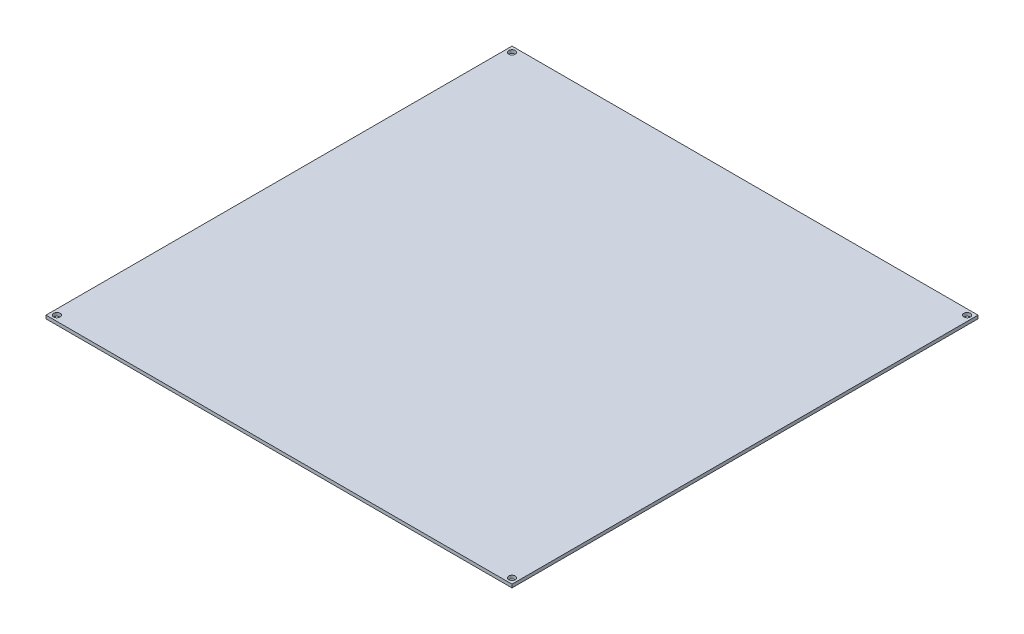
SolidWorks part; units mm, degrees
ref_plane "Plan de face" through (0, 0, 0) normal (0, 0, 1) x (1, 0, 0)
ref_plane "Plan de dessus" through (0, 0, 0) normal (0, 1, 0) x (1, 0, 0)
ref_plane "Plan de droite" through (0, 0, 0) normal (1, 0, 0) x (0, 0, -1)
sketch "Esquisse1" plane through (0, 0, 0) normal (0, 1, 0) x (1, 0, 0)
  line L1 (-109.1351, 78.6329) -> (104.8649, 78.6329)
  line L2 (-109.1351, 78.6329) -> (-109.1351, -135.3671)
  line L3 (-109.1351, -135.3671) -> (104.8649, -135.3671)
  line L4 (104.8649, 78.6329) -> (104.8649, -135.3671)
  dimension "D1" = 214
  dimension "D2" = 214
extrude "Boss.-Extru.1" add sketch "Esquisse1" along normal blind 1.5
hole_wizard "Diamètre du perçage Ø3.0 (3)1" positions "Esquisse3" profile "Esquisse4" hole size "Ø3.0" standard "Din" end condition through all
sketch "Esquisse3" plane through (0, 1.5, 0) normal (0, 1, 0) x (1, 0, 0)
  line L0 (-109.1351, -135.3671) -> (104.8649, -135.3671) construction
  line L1 (-109.1351, 78.6329) -> (-109.1351, -135.3671) construction
  line L2 (104.8649, -135.3671) -> (104.8649, 78.6329) construction
  line L3 (104.8649, 78.6329) -> (-109.1351, 78.6329) construction
  point P0 (-106.6351, -132.8671)
  point P2 (-106.6351, 76.1329)
  point P4 (102.3649, 76.1329)
  point P6 (102.3649, -132.8671)
  dimension "D1" = 2.5
  dimension "D2" = 2.5
  dimension "D3" = 2.5
  dimension "D4" = 2.5
  dimension "D5" = 2.5
  dimension "D6" = 2.5
  dimension "D7" = 2.5
  dimension "D8" = 2.5
sketch "Esquisse4" plane through (-106.6351, 1.5, 132.8671) normal (1, 0, 0) x (0, 0, 1)
  line L0 (0, 0) -> (0, 1.5)
  line L1 (0, 1.5) -> (1.5, 1.5)
  line L2 (1.5, 1.5) -> (1.5, 0)
  line L5 (1.5, 0) -> (0, 0)
  line L11 (0, -6.35) -> (0, 107.95) construction
  dimension "Diamètre du perçage jusqu'au prochain" = 3
  dimension "Profondeur du perçage jusqu'au prochain" = 1.5
